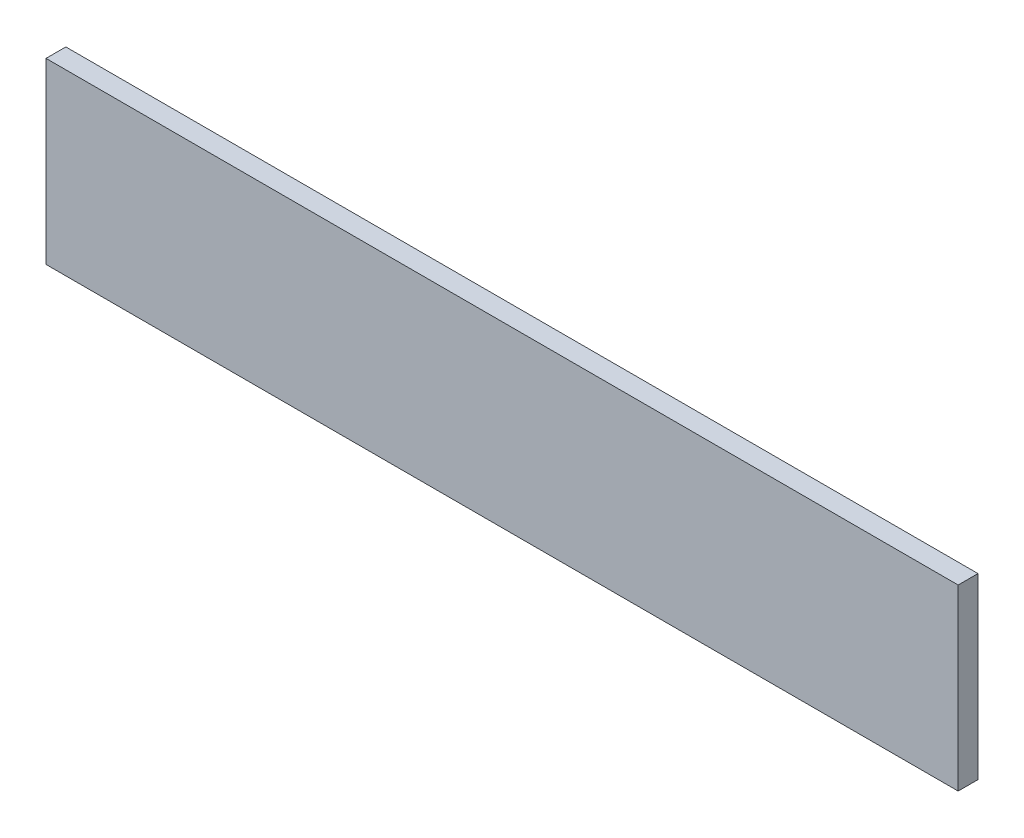
SolidWorks part; units mm, degrees
ref_plane "Front Plane" through (0, 0, 0) normal (0, 0, 1) x (1, 0, 0)
ref_plane "Top Plane" through (0, 0, 0) normal (0, 1, 0) x (1, 0, 0)
ref_plane "Right Plane" through (0, 0, 0) normal (1, 0, 0) x (0, 0, -1)
sketch "Sketch1" plane through (0, 0, 0) normal (0, 0, 1) x (1, 0, 0)
  line L1 (0, 0) -> (292.1, 0)
  line L2 (0, 0) -> (0, 57.15)
  line L3 (0, 57.15) -> (292.1, 57.15)
  line L4 (292.1, 0) -> (292.1, 57.15)
  dimension "D1" = 292.1
  dimension "D2" = 57.15
extrude "Boss-Extrude1" add sketch "Sketch1" along normal blind 6.35 contours L3 L4 L1 L2
